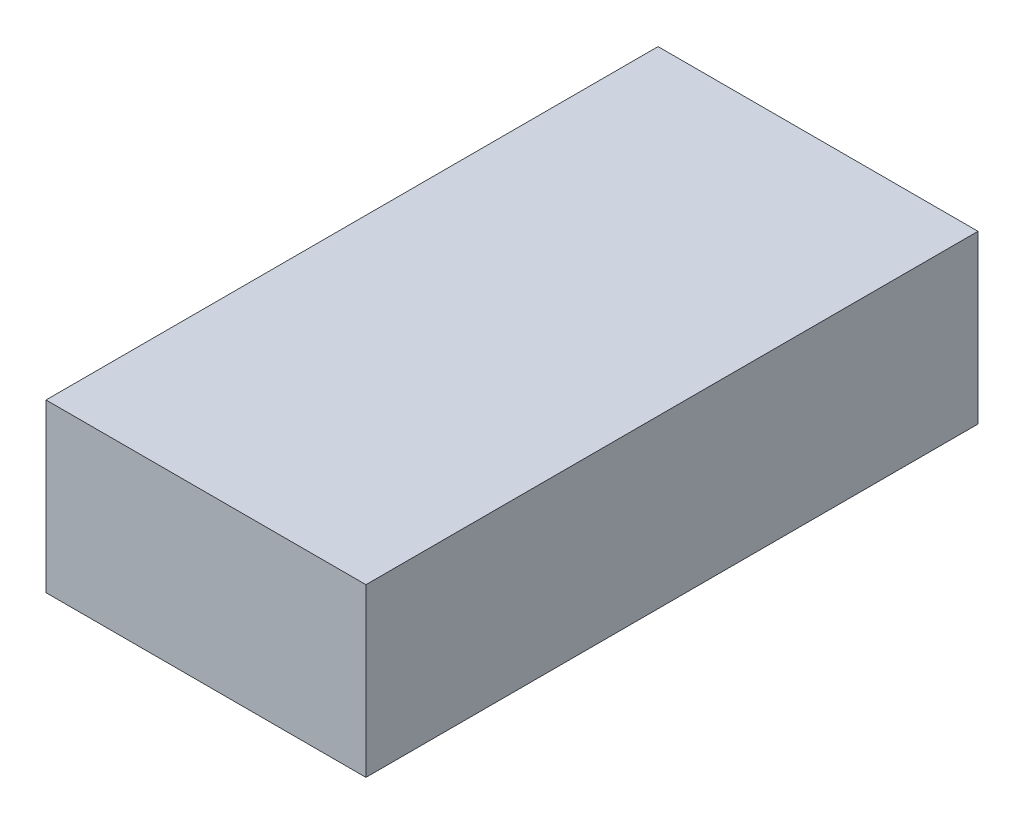
SolidWorks part; units mm, degrees
ref_plane "Front Plane" through (0, 0, 0) normal (0, 0, 1) x (1, 0, 0)
ref_plane "Top Plane" through (0, 0, 0) normal (0, 1, 0) x (1, 0, 0)
ref_plane "Right Plane" through (0, 0, 0) normal (1, 0, 0) x (0, 0, -1)
sketch "Sketch1" plane through (0, 0, 0) normal (0, 1, 0) x (1, 0, 0)
  line L1 (0, 0) -> (73.025, 0)
  line L2 (0, 0) -> (0, 139.7)
  line L3 (0, 139.7) -> (73.025, 139.7)
  line L4 (73.025, 0) -> (73.025, 139.7)
  dimension "D1" = 139.7
  dimension "D2" = 73.025
extrude "Boss-Extrude1" add sketch "Sketch1" along normal blind 38.1
